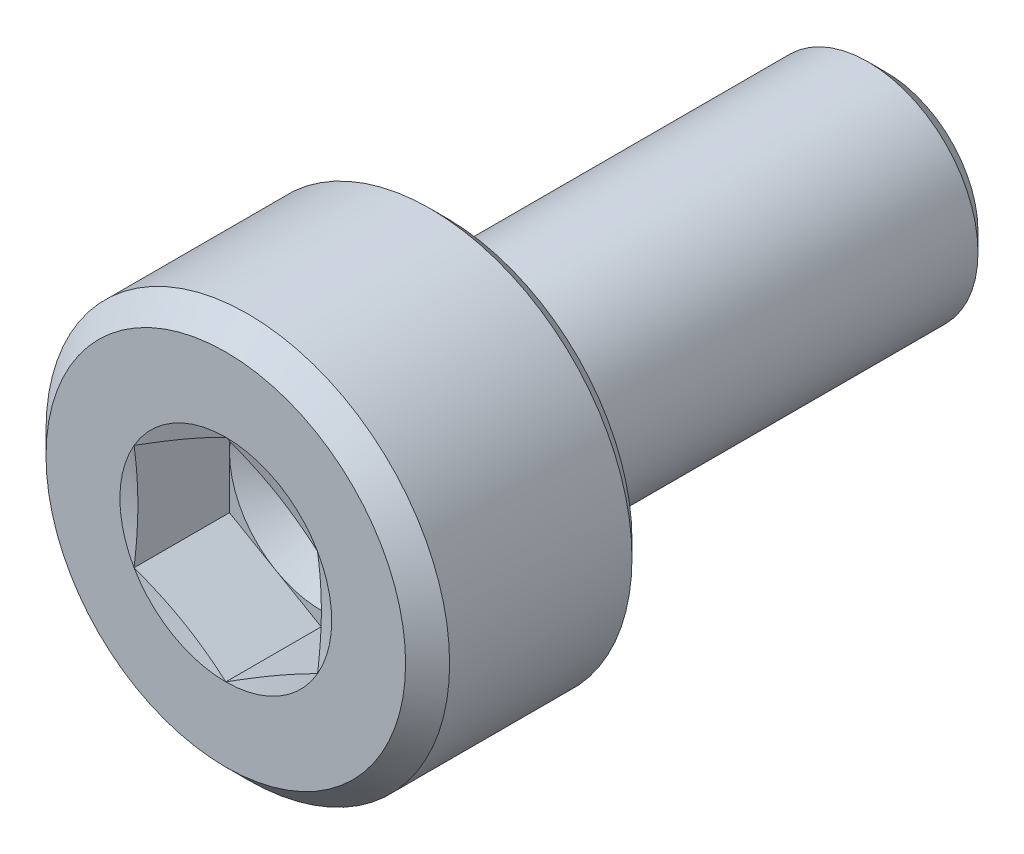
SolidWorks part; units mm, degrees
ref_plane "Front Plane" through (0, 0, 0) normal (0, 0, 1) x (1, 0, 0)
ref_plane "Top Plane" through (0, 0, 0) normal (0, 1, 0) x (1, 0, 0)
ref_plane "Right Plane" through (0, 0, 0) normal (1, 0, 0) x (0, 0, -1)
sketch "Sketch1" plane through (0, 0, 0) normal (1, 0, 0) x (0, 0, -1)
  line L0 (0, 0) -> (12.9407, 0) construction
  line L1 (0, 0) -> (0, 2.45)
  line L2 (0, 2.45) -> (0.3, 2.75)
  line L3 (0.3, 2.75) -> (2.785, 2.75)
  line L4 (3, 2.535) -> (3, 1.8)
  line L5 (3.51, 1.5) -> (8.75, 1.5)
  line L6 (8.75, 1.5) -> (9, 1.25)
  line L7 (9, 1.25) -> (9, 0)
  line L8 (9, 0) -> (0, 0)
  line L9 (2.785, 2.75) -> (3, 2.535)
  line L10 (3.4662, 1.5101) -> (3.0562, 1.7101)
  arc A2 (3.51, 1.5) -> (3.4662, 1.5101) centre (3.51, 1.6) cw
  arc A3 (3.0562, 1.7101) -> (3, 1.8) centre (3.1, 1.8) cw
  point P6 (3, 2.75)
  dimension "R2" = 0.1
  dimension "R1" = 0.1
  dimension "D1" = 45
  dimension "DK" = 5.5
  dimension "D3" = 45
  dimension "length" = 6
  dimension "K" = 3
  dimension "V" = 0.3
  dimension "HOLESIZE" = 3
  dimension "D4" = 2.5
  dimension "D5" = 45
  dimension "DW" = 5.07
  dimension "F" = 0.51
  dimension "DA" = 3.6
revolve "Revolve1" add sketch "Sketch1" angle 360 about L0
cosmetic thread "Cosmetic Thread1" parameters "D1"=4.5, "D2"=3
sketch "Sketch2" plane through (0, 0, 0) normal (0, 0, 1) x (1, 0, 0)
  line L0 (0, 0) -> (0, 1.4434) construction
  line L2 (0, 1.4434) -> (-1.25, 0.7217)
  line L3 (-1.25, 0.7217) -> (-1.25, -0.7217)
  line L4 (-1.25, -0.7217) -> (0, -1.4434)
  line L5 (0, -1.4434) -> (1.25, -0.7217)
  line L6 (1.25, -0.7217) -> (1.25, 0.7217)
  line L7 (1.25, 0.7217) -> (0, 1.4434)
  circle A0 centre (0, 0) radius 1.25 construction
  dimension "S" = 2.5
extrude "Cut-Extrude1" cut sketch "Sketch2" against normal blind 1.3
sketch "Sketch3" plane through (0, 0, 0) normal (1, 0, 0) x (0, 0, -1)
  line L0 (1.3, 0) -> (9, 0) construction
  line L1 (9, -1.25) -> (9, 1.25) construction
  line L2 (1.3, 0) -> (1.3, 1.25)
  line L4 (1.3, 1.25) -> (2.0217, 0)
  line L5 (2.0217, 0) -> (1.3, 0)
  line L6 (0, 2.45) -> (0, -2.45) construction
  dimension "DRILLANG" = 60
  dimension "DRILL DEPTH" = 1.3
  dimension "S2" = 2.5
revolve "Cut-Revolve2" cut sketch "Sketch3" angle 360 about L0
sketch "Sketch4" plane through (0, 0, 0) normal (1, 0, 0) x (0, 0, -1)
  line L0 (0, 0) -> (4.6121, 0) construction
  line L1 (0, 1.4434) -> (0, 1.25)
  line L2 (0, 2.45) -> (0, -2.45) construction
  line L3 (0, 1.25) -> (0.0518, 1.25)
  line L4 (0.0518, 1.25) -> (0, 1.4434)
  point P12 (0.0259, 1.25)
  dimension "D1" = 2.5
  dimension "D2" = 15
revolve "Cut-Revolve3" cut sketch "Sketch4" angle 360 about L0
